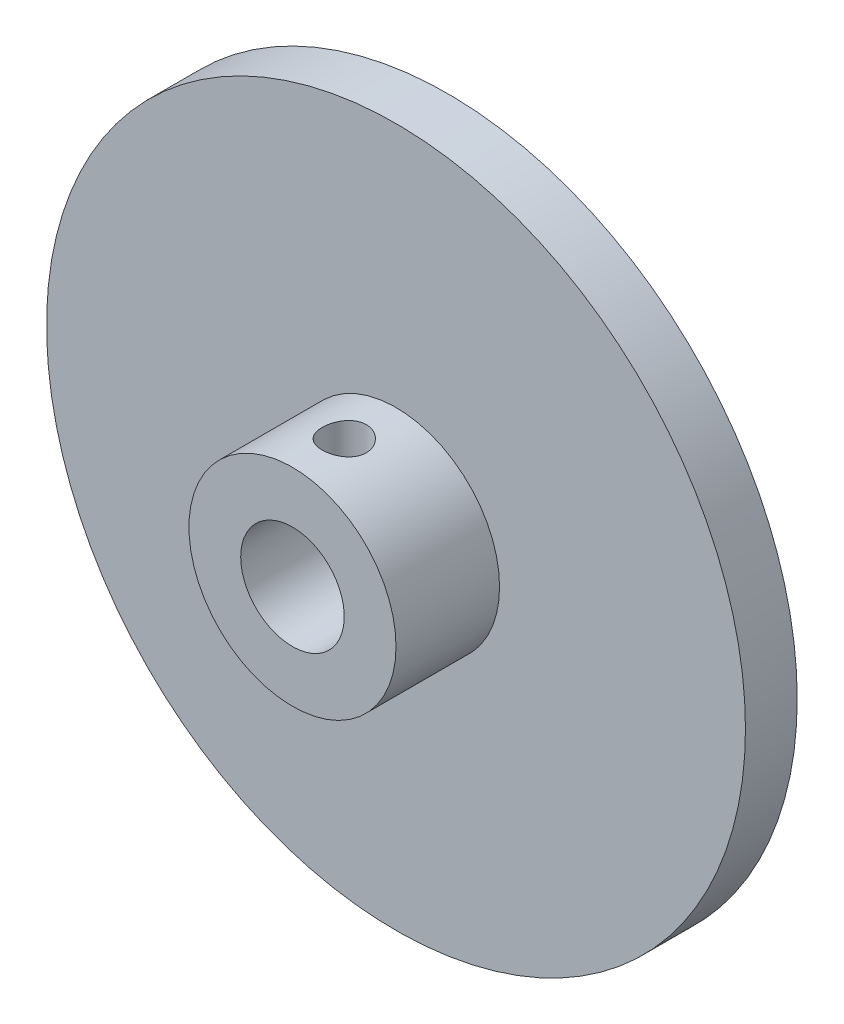
SolidWorks part; units mm, degrees
material "303 Stainless"
ref_plane "Front Plane" through (0, 0, 0) normal (0, 0, 1) x (1, 0, 0)
ref_plane "Top Plane" through (0, 0, 0) normal (0, 1, 0) x (1, 0, 0)
ref_plane "Right Plane" through (0, 0, 0) normal (1, 0, 0) x (0, 0, -1)
sketch "Sketch1" plane through (0, 0, 0) normal (0, 0, 1) x (1, 0, 0)
  circle A0 centre (0, 0) radius 21.4312
  dimension "D1" = 42.8625
extrude "Boss-Extrude1" add sketch "Sketch1" along normal blind 3.175
sketch "Sketch2" plane through (0, 0, 3.175) normal (0, 0, 1) x (1, 0, 0)
  circle A0 centre (0, 0) radius 6.35
  dimension "D1" = 12.7
extrude "Boss-Extrude2" add sketch "Sketch2" along normal blind 6.35
sketch "Sketch3" plane through (0, 0, 0) normal (0, 0, -1) x (-1, 0, 0)
  circle A0 centre (0, 0) radius 3.175
  dimension "D1" = 6.35
extrude "Cut-Extrude1" cut sketch "Sketch3" against normal through all
ref_plane "Plane1" through (0, 6.35, 0) normal (0, 1, 0) x (1, 0, 0)
hole_wizard "#6-32 Tapped Hole1" positions "Sketch7" profile "Sketch6" tap size "#6-32" standard "ANSI Inch"
sketch "Sketch7" plane through (0, 6.35, 0) normal (0, 1, 0) x (1, 0, 0)
  line L0 (-6.35, -9.525) -> (6.35, -9.525) construction
  line L1 (-6.35, -3.175) -> (6.35, -3.175) construction
  line L2 (-6.35, -9.525) -> (6.35, -9.525)
  line L3 (-6.35, -3.175) -> (6.35, -3.175)
  line L4 (6.35, -3.175) -> (6.35, -9.525)
  point P0 (0, -6.35)
  point P11 (6.35, -6.35)
  point P13 (0, -3.175)
sketch "Sketch6" plane through (0, 6.35, 6.35) normal (1, 0, 0) x (0, 0, 1)
  line L0 (0, 0) -> (0, 3.175)
  line L1 (0, 3.175) -> (1.3525, 3.175)
  line L2 (1.3525, 3.175) -> (1.3525, 0)
  line L5 (1.3525, 0) -> (0, 0)
  line L11 (0, -6.35) -> (0, 107.95) construction
  dimension "Thru Tap Drill Dia." = 2.7051
  dimension "Thru Tap Drill Depth" = 3.175
cosmetic thread "Hole Thread1" parameters "D2"=3.5052
equation "\"pitch\"= 1.6875"
equation "\"bore\"= .25"
equation "\"hub\"= .5"
equation "\"hub l\"= .25"
equation "\"D1@Sketch1\"=\"pitch\""
equation "\"D1@Sketch2\"=\"hub\""
equation "\"D1@Boss-Extrude2\"=\"hub l\""
equation "\"D1@Sketch3\"=\"bore\""
equation "\"face\"= .125"
equation "\"D1@Boss-Extrude1\"=\"face\""
